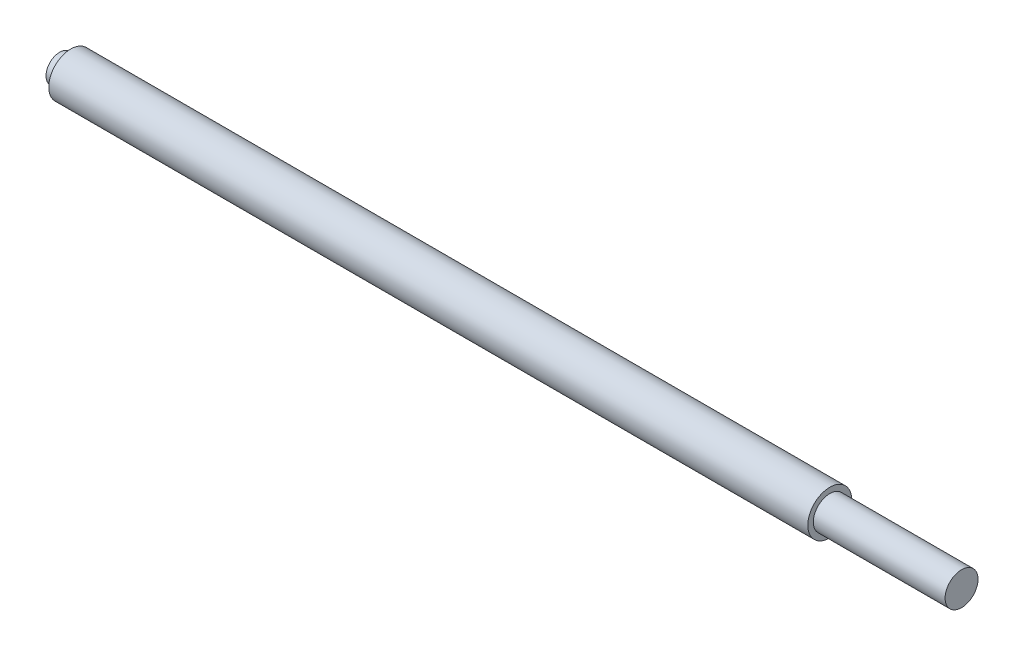
SolidWorks part; units mm, degrees
material "Plain Carbon Steel"
ref_plane "Front Plane" through (0, 0, 0) normal (0, 0, 1) x (1, 0, 0)
ref_plane "Top Plane" through (0, 0, 0) normal (0, 1, 0) x (1, 0, 0)
ref_plane "Right Plane" through (0, 0, 0) normal (1, 0, 0) x (0, 0, -1)
sketch "Sketch2" plane through (0, 0, 0) normal (0, 1, 0) x (1, 0, 0)
  line L6 (445.2264, 9.525) -> (445.2264, 12.7)
  line L7 (521.4264, 9.525) -> (445.2264, 9.525)
  line L8 (521.4264, 0) -> (521.4264, 9.525)
  line L9 (0, 7.9375) -> (0, 0)
  line L10 (6.35, 12.7) -> (445.2264, 12.7)
  line L11 (0, 0) -> (521.4264, 0)
  line L12 (0, 7.9375) -> (6.35, 7.9375)
  line L13 (6.35, 7.9375) -> (6.35, 12.7)
  dimension "D1" = 521.4264
  dimension "D2" = 76.2
  dimension "D3" = 9.525
  dimension "D4" = 12.7
  dimension "D5" = 6.35
  dimension "D6" = 7.9375
revolve "Revolve1" add sketch "Sketch2" angle 360 about L11
sketch "Sketch3" plane through (0, 0, 0) normal (0, 1, 0) x (1, 0, 0)
  line L5 (521.4264, 0) -> (209.0064, 0) construction
  line L7 (209.0064, 0) -> (209.0064, 11.1125) construction
  line L9 (196.3064, 9.525) -> (221.7064, 9.525)
  line L10 (196.3064, 9.525) -> (196.3064, 12.7)
  line L11 (196.3064, 12.7) -> (221.7064, 12.7)
  line L12 (221.7064, 9.525) -> (221.7064, 12.7)
  line L13 (196.3064, 9.525) -> (221.7064, 12.7) construction
  line L14 (196.3064, 12.7) -> (221.7064, 9.525) construction
  line L15 (521.4264, -9.525) -> (521.4264, 9.525) construction
  line L16 (445.2264, 12.7) -> (6.35, 12.7) construction
  point P2 (541.1366, 0)
  point P3 (0, 0)
  point P10 (0, 0)
  dimension "D1" = 312.42
  dimension "D2" = 25.4
  dimension "D3" = 3.175
extrude "Cut-Extrude1" cut sketch "Sketch3" against normal through all both and the other way through all
